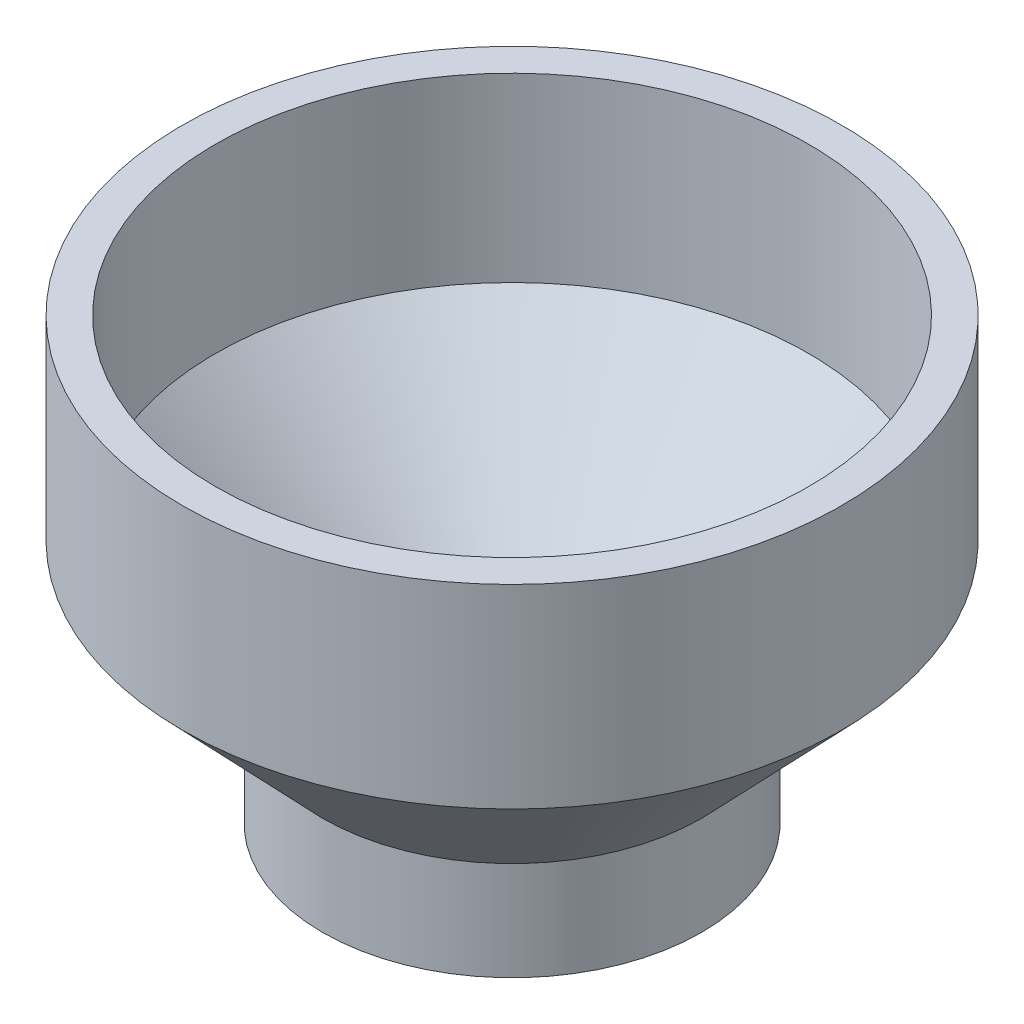
SolidWorks part; units mm, degrees
ref_plane "Front" through (0, 0, 0) normal (0, 0, 1) x (1, 0, 0)
ref_plane "Top" through (0, 0, 0) normal (0, 1, 0) x (1, 0, 0)
ref_plane "Right" through (0, 0, 0) normal (1, 0, 0) x (0, 0, -1)
sketch "Sketch1" plane through (0, 0, 0) normal (0, 0, 1) x (1, 0, 0)
  line L0 (-30.1625, 0) -> (-30.1625, 21.59)
  line L1 (-30.1625, 21.59) -> (-57.15, 49.784)
  line L2 (-57.15, 49.784) -> (-57.15, 84.709)
  line L3 (0, 0) -> (0, -10.4431) construction
  dimension "D1" = 114.3
  dimension "D2" = 60.325
  dimension "D3" = 84.709
  dimension "D4" = 34.925
  dimension "D5" = 21.59
revolve "Revolve-Thin1" add sketch "Sketch1" angle 360 about L3 wall 6.35
